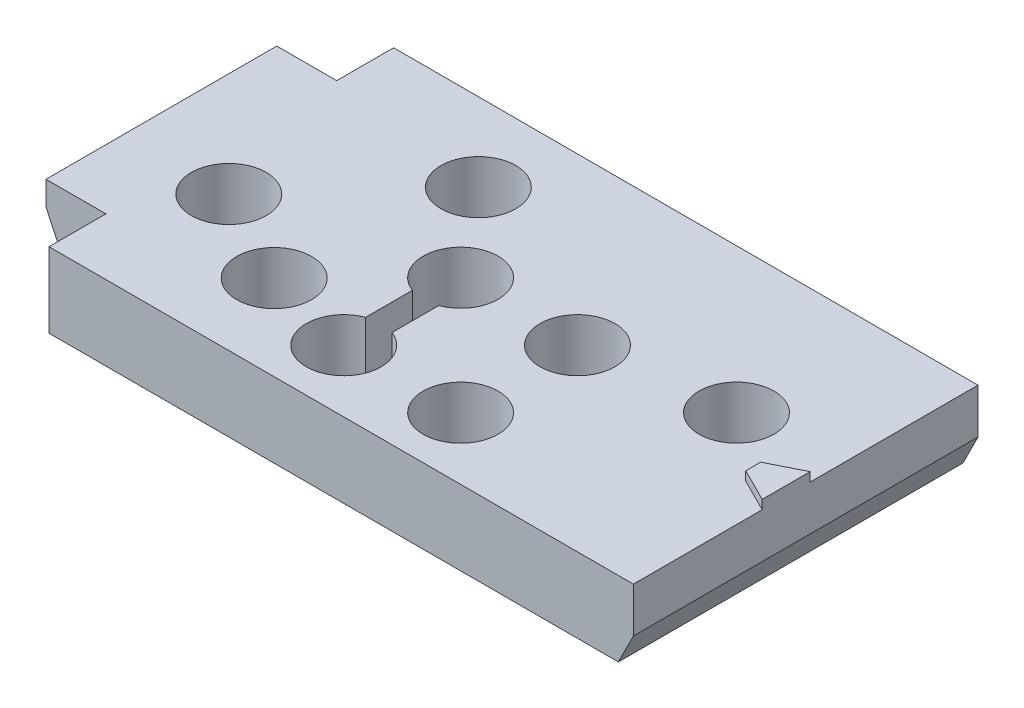
SolidWorks part; units mm, degrees
ref_plane "Front Plane" through (0, 0, 0) normal (0, 0, 1) x (1, 0, 0)
ref_plane "Top Plane" through (0, 0, 0) normal (0, 1, 0) x (1, 0, 0)
ref_plane "Right Plane" through (0, 0, 0) normal (1, 0, 0) x (0, 0, -1)
sketch "Sketch1" plane through (0, 0, 0) normal (0, 1, 0) x (1, 0, 0)
  line L0 (569.9673, 1345.2069) -> (2943.0364, 1386.6289) construction
  line L1 (46.9196, 30.9707) -> (46.9196, 27.0083)
  line L2 (77.8491, 47.9832) -> (28.3191, 47.9832)
  line L3 (77.8491, 47.9832) -> (77.8491, 18.7732)
  line L4 (77.8491, 18.7732) -> (28.3191, 18.7732)
  line L5 (28.3191, 47.9832) -> (28.3191, 18.7732) construction
  line L6 (23.2391, 43.1572) -> (28.3191, 43.1572)
  line L7 (23.2391, 43.1572) -> (23.2391, 23.5992)
  line L8 (23.2391, 23.5992) -> (28.3191, 23.5992)
  line L9 (28.3191, 43.1572) -> (28.3191, 23.5992) construction
  line L10 (44.8622, 33.9425) -> (61.1182, 33.9425) construction
  line L11 (49.1548, 27.0083) -> (49.1548, 30.9707)
  line L12 (48.0372, 37.1175) -> (48.0372, 20.8615) construction
  line L13 (46.9196, 28.9895) -> (49.1548, 28.9895) construction
  line L14 (57.9432, 37.1175) -> (57.9432, 20.8615) construction
  line L15 (23.2391, 33.3782) -> (28.3191, 33.3782) construction
  line L16 (559.7667, 1221.4994) -> (2735.7667, 1221.4994) construction
  line L17 (44.8622, 24.0365) -> (61.1182, 24.0365) construction
  line L18 (44.0402, 38.7966) -> (47.0851, 36.9714) construction
  line L19 (32.0692, 30.2631) -> (40.1618, 26.0146) construction
  line L20 (40.1618, 26.0146) -> (48.0372, 24.0365) construction
  line L21 (57.9432, 33.9425) -> (69.6313, 35.7318) construction
  line L28 (28.3191, 47.9832) -> (28.3191, 43.1572)
  line L29 (28.3191, 23.5992) -> (28.3191, 18.7732)
  circle A0 centre (42.1431, 41.3424) radius 3.175
  arc A1 (49.1548, 30.9707) -> (46.9196, 30.9707) centre (48.0372, 33.9425) ccw
  arc A2 (46.9196, 27.0083) -> (49.1548, 27.0083) centre (48.0372, 24.0365) ccw
  circle A3 centre (40.1618, 26.0146) radius 3.175
  circle A4 centre (32.0692, 30.2631) radius 3.175
  circle A5 centre (57.9432, 24.0365) radius 3.175
  circle A6 centre (57.9432, 33.9425) radius 3.175
  circle A7 centre (69.6313, 35.7318) radius 3.175
  point P10 (42.1431, 41.3424)
  point P11 (40.1618, 26.0146)
  point P12 (32.0692, 30.2631)
  point P13 (48.0372, 33.9425)
  point P14 (48.0372, 24.0365)
  point P15 (57.9432, 24.0365)
  point P16 (57.9432, 33.9425)
  point P17 (69.6313, 35.7318)
  point P46 (28.3191, 33.3782)
  point P47 (23.2391, 33.3782)
  dimension "D1" = 6.35
  dimension "D2" = 16.256
  dimension "D3" = 29.21
  dimension "D4" = 54.61
  dimension "D5" = 49.53
  dimension "D6" = 19.558
  dimension "D7" = 3.55
  dimension "D8" = 9.14
  dimension "D9" = 8.12
  dimension "D10" = 1.1176
  dimension "D11" = 1.1176
extrude "Boss-Extrude1" add sketch "Sketch1" against normal blind 6.35 contours L6 L28 L2 L3 L4 L29 L8 L7
sketch "Sketch2" plane through (0, 0, 0) normal (0, 1, 0) x (1, 0, 0)
  line L0 (46.9196, 30.9707) -> (46.9196, 27.0083) construction
  line L1 (49.1548, 27.0083) -> (49.1548, 30.9707) construction
  line L2 (46.9196, 30.9707) -> (46.9196, 27.0083)
  line L3 (49.1548, 27.0083) -> (49.1548, 30.9707)
  circle A0 centre (42.1431, 41.3424) radius 3.175 construction
  circle A1 centre (48.0372, 33.9425) radius 3.175 construction
  circle A2 centre (32.0692, 30.2631) radius 3.175 construction
  circle A3 centre (40.1618, 26.0146) radius 3.175 construction
  circle A4 centre (48.0372, 24.0365) radius 3.175 construction
  circle A5 centre (57.9432, 33.9425) radius 3.175 construction
  circle A6 centre (57.9432, 24.0365) radius 3.175 construction
  circle A7 centre (69.6313, 35.7318) radius 3.175 construction
  circle A8 centre (42.1431, 41.3424) radius 3.175
  arc A9 (49.1548, 30.9707) -> (46.9196, 30.9707) centre (48.0372, 33.9425) ccw
  circle A10 centre (32.0692, 30.2631) radius 3.175
  circle A11 centre (40.1618, 26.0146) radius 3.175
  arc A12 (46.9196, 27.0083) -> (49.1548, 27.0083) centre (48.0372, 24.0365) ccw
  circle A13 centre (57.9432, 33.9425) radius 3.175
  circle A14 centre (57.9432, 24.0365) radius 3.175
  circle A15 centre (69.6313, 35.7318) radius 3.175
extrude "Cut-Extrude1" cut sketch "Sketch2" against normal blind 5.588
sketch "Sketch3" plane through (0, 0, 0) normal (0, 1, 0) x (1, 0, 0)
  line L0 (77.8491, 33.7592) -> (75.0551, 32.3622)
  line L1 (75.0551, 32.3622) -> (75.0551, 31.0922)
  line L2 (75.0551, 31.0922) -> (77.8491, 29.6952)
  line L3 (77.8491, 47.9832) -> (77.8491, 18.7732) construction
  line L4 (77.8491, 47.9832) -> (77.8491, 18.7732) construction
  line L5 (77.8491, 33.7592) -> (77.8491, 29.6952)
  dimension "D1" = 4.064
  dimension "D2" = 2.794
  dimension "D3" = 1.27
  dimension "D4" = 10.922
extrude "Boss-Extrude2" add sketch "Sketch3" along normal blind 0.762
sketch "Sketch4" plane through (0, 0, 0) normal (0, 1, 0) x (1, 0, 0)
  circle A0 centre (69.6313, 35.7318) radius 1.016
  circle A1 centre (40.1618, 26.0146) radius 1.016
  dimension "D1" = 2.032
extrude "Cut-Extrude2" cut sketch "Sketch4" against normal through all
sketch "Sketch5" plane through (0, 0, -18.7732) normal (0, 0, 1) x (1, 0, 0)
  line L0 (77.8491, -3.81) -> (76.5791, -6.35)
  line L1 (77.8491, -6.35) -> (77.8491, 0) construction
  line L2 (77.8491, -6.35) -> (28.3191, -6.35) construction
  line L3 (76.5791, -6.35) -> (77.8491, -6.35)
  line L4 (77.8491, -6.35) -> (77.8491, -3.81)
  dimension "D1" = 1.27
  dimension "D2" = 2.54
extrude "Cut-Extrude3" cut sketch "Sketch5" against normal through all
sketch "Sketch6" plane through (0, 0, -23.5992) normal (0, 0, 1) x (1, 0, 0)
  line L0 (25.2711, -6.35) -> (23.2391, -2.032)
  line L2 (23.2391, -6.35) -> (23.2391, 0) construction
  line L3 (23.2391, -2.032) -> (23.2391, -6.35)
  line L4 (23.2391, -6.35) -> (25.2711, -6.35)
  dimension "D1" = 4.318
  dimension "D2" = 2.032
extrude "Cut-Extrude4" cut sketch "Sketch6" against normal through all
